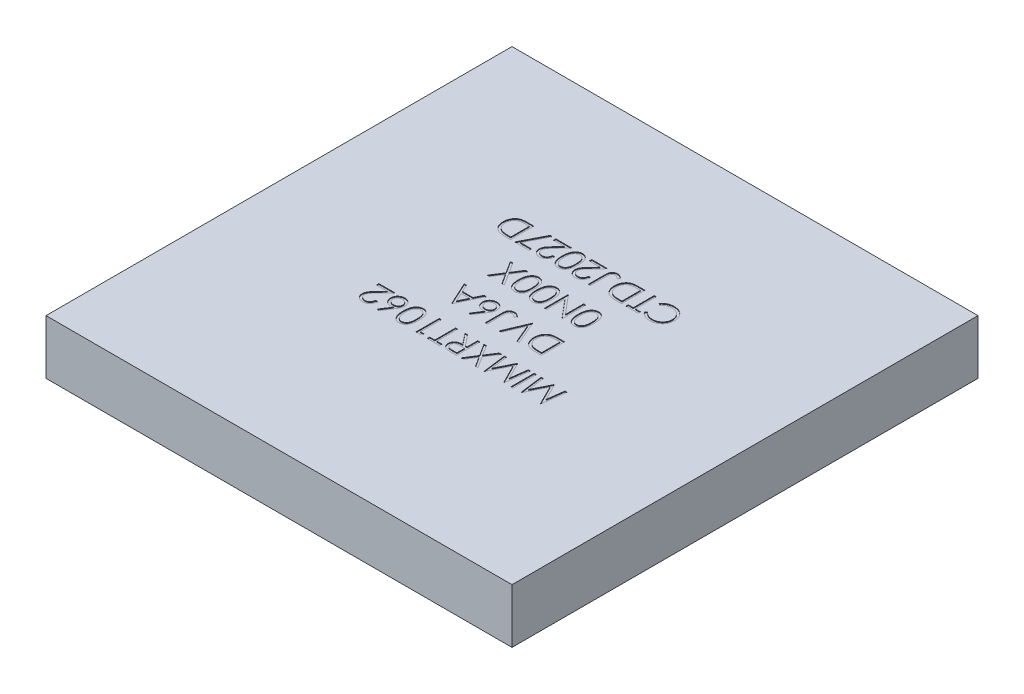
SolidWorks part; units mm, degrees
ref_plane "Front Plane" through (0, 0, 0) normal (0, 0, 1) x (1, 0, 0)
ref_plane "Top Plane" through (0, 0, 0) normal (0, 1, 0) x (1, 0, 0)
ref_plane "Right Plane" through (0, 0, 0) normal (1, 0, 0) x (0, 0, -1)
sketch "BaseS" plane through (0, 0, 0) normal (0, 1, 0) x (1, 0, 0)
  line L1 (-6, 6) -> (6, 6)
  line L2 (-6, 6) -> (-6, -6)
  line L3 (-6, -6) -> (6, -6)
  line L4 (6, 6) -> (6, -6)
  line L5 (-6, 6) -> (6, -6) construction
  line L6 (-6, -6) -> (6, 6) construction
  point P0 (0, 0)
  dimension "Dim" = 12
extrude "Base" add sketch "BaseS" along normal blind 1.4
sketch "PartNumberS" plane through (0, 1.4, 0) normal (0, 1, 0) x (1, 0, 0)
  line L0 (6, -1) -> (-6, -1) construction
  line L1 (6, -6) -> (6, 6) construction
  line L2 (-6, 6) -> (-6, -6) construction
  line L3 (-6, -6) -> (6, -6) construction
  text T0 "MIMXRT1062\r\nDVJ6A\r\n0N00X\r\nCTDJ2027D" font "Century Gothic" height 0.6
  dimension "YDim" = 5
extrude "PartNumber" cut sketch "PartNumberS" against normal blind 0.02
